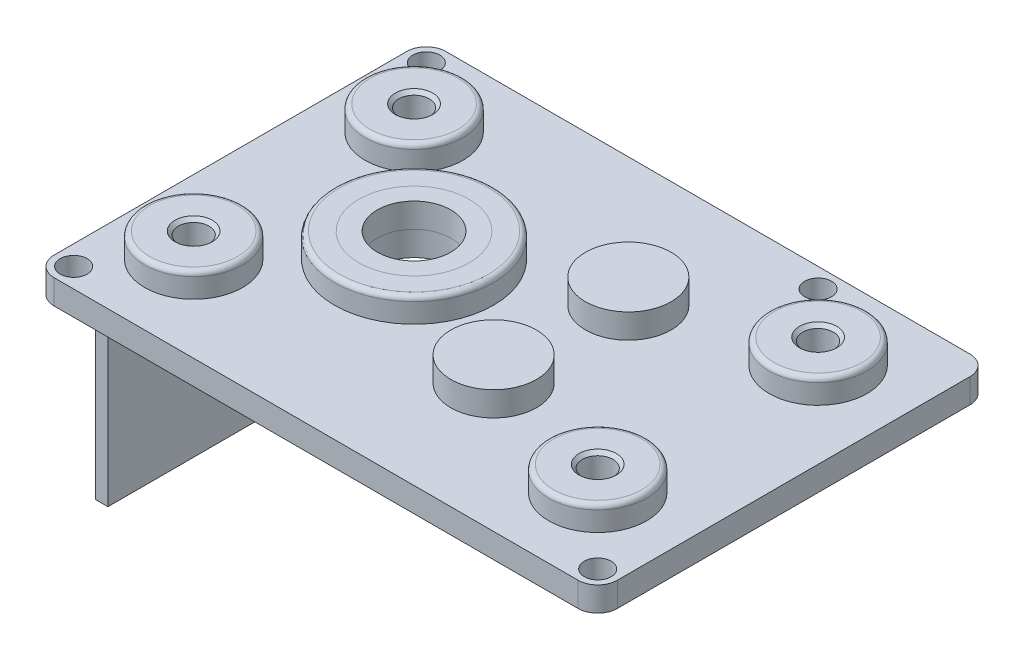
SolidWorks part; units mm, degrees
material "201.0-T7 Insulated Mold Casting (SS)"
ref_plane "Front Plane" through (0, 0, 0) normal (0, 0, 1) x (1, 0, 0)
ref_plane "Top Plane" through (0, 0, 0) normal (0, 1, 0) x (1, 0, 0)
ref_plane "Right Plane" through (0, 0, 0) normal (1, 0, 0) x (0, 0, -1)
sketch "Sketch2" plane through (0, 0, 0) normal (0, 1, 0) x (1, 0, 0)
  line L0 (0, 0) -> (-15, 0) construction
  line L1 (-15, 16) -> (31, 16)
  line L2 (-15, 16) -> (-15, -16)
  line L3 (-15, -16) -> (31, -16)
  line L4 (31, 16) -> (31, -16)
  dimension "D1" = 32
  dimension "D2" = 46
  dimension "D3" = 15
extrude "Boss-Extrude2" add sketch "Sketch2" along normal blind 2
sketch "Sketch6" plane through (0, 2, 0) normal (0, 1, 0) x (1, 0, 0)
  circle A0 centre (0, 0) radius 3
  dimension "D1" = 6
extrude "Cut-Extrude1" cut sketch "Sketch6" against normal through all
sketch "Sketch7" plane through (0, 2, 0) normal (0, 1, 0) x (1, 0, 0)
  circle A0 centre (0, 0) radius 4.5
  circle A1 centre (0, 0) radius 3
  circle A2 centre (0, 0) radius 3 construction
  dimension "D1" = 9
extrude "Boss-Extrude4" add sketch "Sketch7" along normal blind 2 separate body
sketch "Sketch8" plane through (0, 2, 0) normal (0, 1, 0) x (1, 0, 0)
  circle A0 centre (0, 0) radius 4.5
  circle A1 centre (0, 0) radius 4.5 construction
  circle A2 centre (0, 0) radius 6.5
  dimension "D1" = 13
extrude "Boss-Extrude5" add sketch "Sketch8" along normal blind 2 separate body
sketch "Sketch3" plane through (0, 2, 0) normal (0, 1, 0) x (1, 0, 0)
  line L0 (-15, 0) -> (31, 0) construction
  line L1 (-15, 16) -> (-15, -16) construction
  line L2 (31, -16) -> (31, 16) construction
  line L3 (8, -16) -> (8, 16) construction
  line L4 (-15, -16) -> (31, -16) construction
  line L5 (31, 16) -> (-15, 16) construction
  circle A0 centre (-9, 9) radius 4
  circle A1 centre (0, 0) radius 3 construction
  dimension "D1" = 8
  dimension "D2" = 9
  dimension "D3" = 9
extrude "Boss-Extrude3" add sketch "Sketch3" along normal blind 2
fillet "Fillet3" radius 0.4 1 edges at (0, 4, 6.5)
ref_plane "MP HORZ HOLES" through (8, 0, 0) normal (-1, 0, 0) x (0, 0, 1)
hole_wizard "M3x0.5 Tapped Hole1" positions "Sketch5" profile "Sketch4" tap size "M3x0.5" standard "ANSI Metric" end condition through all
sketch "Sketch5" plane through (0, 4, 0) normal (0, 1, 0) x (1, 0, 0)
  point P0 (-9, 9)
sketch "Sketch4" plane through (-9, 4, -9) normal (1, 0, 0) x (0, 0, 1)
  line L0 (0, 0) -> (0, 4)
  line L1 (0, 4) -> (1.25, 4)
  line L2 (1.25, 4) -> (1.25, 0.275)
  line L3 (1.25, 0.275) -> (1.525, 0)
  line L5 (1.525, 0) -> (0, 0)
  line L6 (-1.25, 0.275) -> (-1.525, 0) construction
  line L11 (0, -6.35) -> (0, 107.95) construction
  dimension "Thread Major Dia." = 2.5
  dimension "Thru Tap Drill Depth" = 4
  dimension "Near C'Sink Dia." = 3.05
  dimension "Near C'Sink Angle" = 90
pattern_linear "LPattern1" count 2 spacing 33 along (1, 0, 0) of "M3x0.5 Tapped Hole1", "Boss-Extrude3"
sketch "Sketch9" plane through (0, 2, 0) normal (0, 1, 0) x (1, 0, 0)
  line L0 (0, 0) -> (12, 0) construction
  line L1 (12, 0) -> (12, 5.5) construction
  circle A0 centre (12, 5.5) radius 3.5
  dimension "D1" = 7
  dimension "D2" = 12
  dimension "D3" = 5.5
extrude "Boss-Extrude6" add sketch "Sketch9" along normal blind 2
mirror "Mirror2" about plane through (0, 0, 0) normal (0, 0, 1) of "LPattern1", "Boss-Extrude3", "M3x0.5 Tapped Hole1"
mirror "Mirror3" about plane through (0, 0, 0) normal (0, 0, 1) of "Boss-Extrude6"
hole_wizard "M2 Clearance Hole1" positions "Sketch11" profile "Sketch10" hole size "M2" standard "ANSI Metric" end condition through all
sketch "Sketch11" plane through (0, 2, 0) normal (0, 1, 0) x (1, 0, 0)
  line L0 (-13.4, 14.4) -> (18.6, 14.4) construction
  line L2 (31, 16) -> (-15, 16) construction
  line L3 (-15, 16) -> (-15, -16) construction
  line L5 (-15, -16) -> (31, -16) construction
  line L6 (29.4, -14.4) -> (-13.4, -14.4) construction
  line L7 (-13.4, 14.4) -> (-13.4, -14.4) construction
  line L9 (31, -16) -> (31, 16) construction
  point P0 (-13.4, 14.4)
  point P4 (18.6, 14.4)
  point P6 (29.4, -14.4)
  point P23 (-13.4, -14.4)
  dimension "D1" = 1.6
  dimension "D2" = 1.6
  dimension "D3" = 1.6
  dimension "D4" = 1.6
  dimension "D5" = 32
sketch "Sketch10" plane through (-13.4, 2, -14.4) normal (1, 0, 0) x (0, 0, 1)
  line L0 (0, 0) -> (0, 2)
  line L1 (0, 2) -> (1.1, 2)
  line L2 (1.1, 2) -> (1.1, 0)
  line L5 (1.1, 0) -> (0, 0)
  line L11 (0, -6.35) -> (0, 107.95) construction
  dimension "Thru Hole Dia." = 2.2
  dimension "Thru Hole Depth" = 2
fillet "Fillet1" radius 1.6 4 edges at (31, 1, -16) (31, 1, 16) (-15, 1, -16) (-15, 1, 16)
sketch "Sketch12" plane through (0, 0, 0) normal (0, -1, 0) x (1, 0, 0)
  line L0 (-15, -14.4) -> (-15, 14.4) construction
  line L1 (-14, -11) -> (-15, -11)
  line L2 (-14, -11) -> (-14, 11)
  line L3 (-14, 11) -> (-15, 11)
  line L4 (-15, -11) -> (-15, 11)
  line L5 (-14, -11) -> (-15, 11) construction
  line L6 (-14, 11) -> (-15, -11) construction
  line L7 (0, 0) -> (-14.5, 0) construction
  point P0 (-14.5, 0)
  dimension "D1" = 1
  dimension "D2" = 22
extrude "Boss-Extrude7" add sketch "Sketch12" along normal blind 17
fillet "Fillet5" radius 0.4 4 edges at (24, 4, 5) (-9, 4, 5) (24, 4, -5) (-9, 4, -5)
